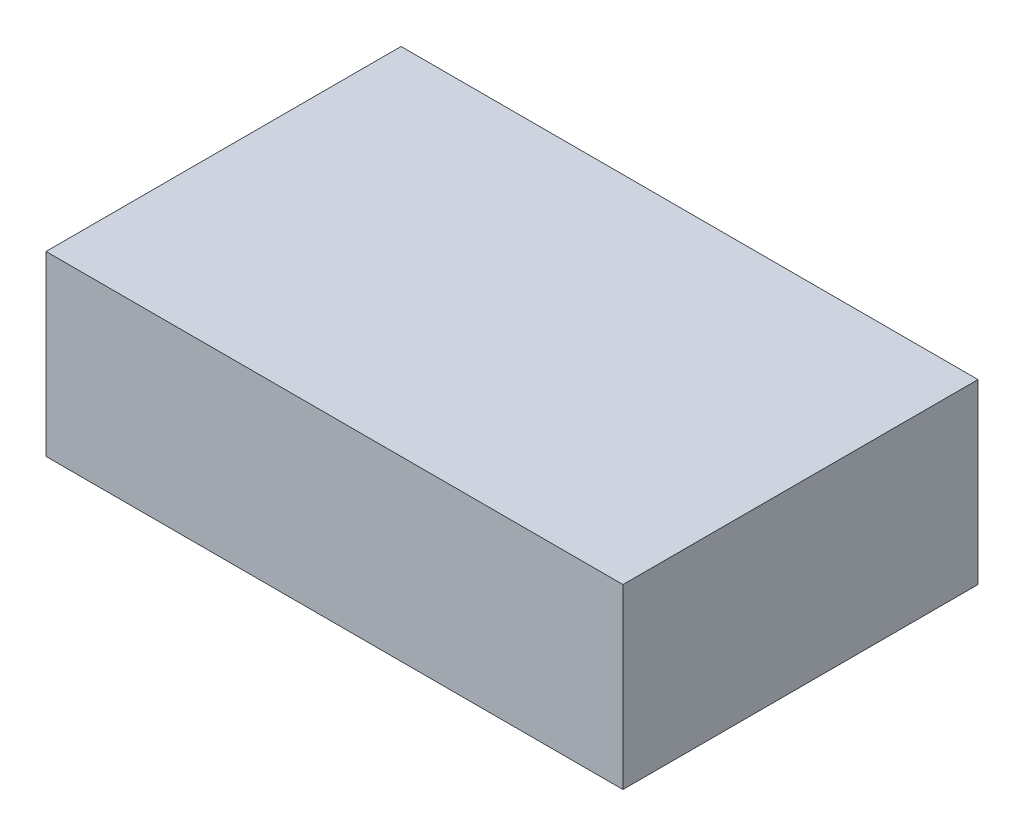
SolidWorks part; units mm, degrees
ref_plane "Front" through (0, 0, 0) normal (0, 0, 1) x (1, 0, 0)
ref_plane "Top" through (0, 0, 0) normal (0, 1, 0) x (1, 0, 0)
ref_plane "Right" through (0, 0, 0) normal (1, 0, 0) x (0, 0, -1)
sketch "Sketch1" plane through (0, 0, 0) normal (0, 1, 0) x (1, 0, 0)
  line L1 (0, 0) -> (2.6, 0)
  line L2 (0, 0) -> (0, 1.6)
  line L3 (0, 1.6) -> (2.6, 1.6)
  line L4 (2.6, 0) -> (2.6, 1.6)
  line L5 (0, 0) -> (2.6, 1.6) construction
  line L6 (0, 1.6) -> (2.6, 0) construction
  point P4 (1.3, 0.8)
  dimension "D1" = 2.6
  dimension "D2" = 1.6
  dimension "D3" = 1.6
extrude "Boss-Extrude1" add sketch "Sketch1" along normal blind 0.8 contours L3 L4 L1 L2
ref_plane "Plane1" through (2.6, 0, 0) normal (0, -1, 0) x (-1, 0, 0)
